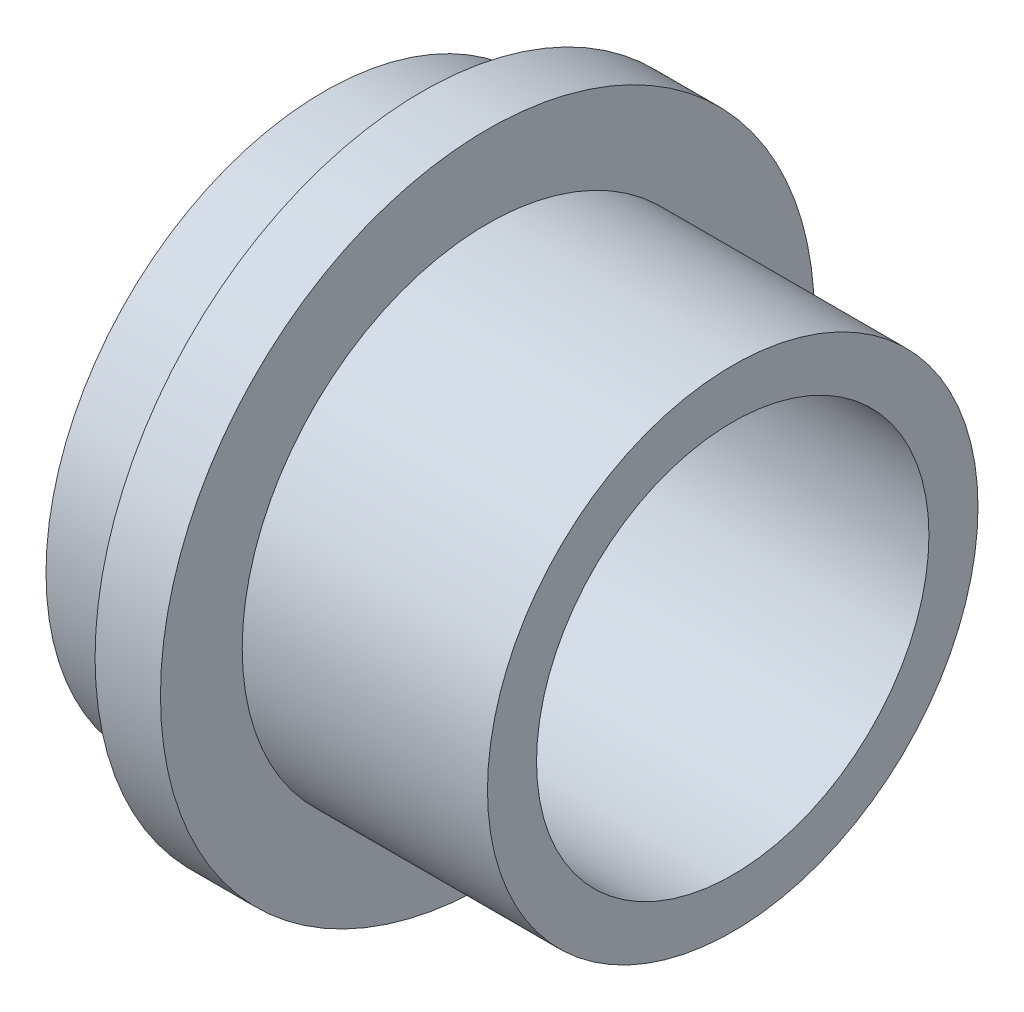
SolidWorks part; units mm, degrees
ref_plane "Face" through (0, 0, 0) normal (0, 0, 1) x (1, 0, 0)
ref_plane "Dessus" through (0, 0, 0) normal (0, 1, 0) x (1, 0, 0)
ref_plane "Droite" through (0, 0, 0) normal (1, 0, 0) x (0, 0, -1)
sketch "Esquisse1" plane through (0, 0, 0) normal (0, 0, 1) x (1, 0, 0)
  line L0 (-59.6035, 0) -> (58.8071, 0) construction
  line L1 (0, 0) -> (0, 8.5)
  line L2 (0, 8.5) -> (3, 8.5)
  line L3 (3, 8.5) -> (3, 9.0937)
  line L4 (3, 9.0937) -> (3, 10)
  line L5 (3, 10) -> (5, 10)
  line L6 (5, 10) -> (5, 7.5)
  line L7 (5, 7.5) -> (12.5, 7.5)
  line L8 (12.5, 7.5) -> (12.5, 0)
  line L9 (12.5, 0) -> (0, 0)
  dimension "D1" = 8.5
  dimension "D2" = 10
  dimension "D3" = 7.5
  dimension "D4" = 3
  dimension "D5" = 2
  dimension "D6" = 7.5
revolve "Révolution1" add sketch "Esquisse1" angle 360 about L0
sketch "Esquisse2" plane through (0, 0, 0) normal (-1, 0, 0) x (0, 0, 1)
  line L0 (-6.6668, 0) -> (7.051, 0) construction
  line L1 (0, 6.9357) -> (0, -4.6302) construction
  line L3 (-4, 4) -> (4, 4)
  line L4 (-4, 4) -> (-4, -4)
  line L5 (-4, -4) -> (4, -4)
  line L6 (4, 4) -> (4, -4)
  dimension "D1" = 8
  dimension "D2" = 8
extrude "Enlèv. mat.-Extru.1" cut sketch "Esquisse2" against normal through all
sketch "Esquisse3" plane through (12.5, 0, 0) normal (1, 0, 0) x (0, 0, -1)
  circle A0 centre (0, 0) radius 6
  dimension "D1" = 12
extrude "Enlèv. mat.-Extru.2" cut sketch "Esquisse3" against normal blind 10
